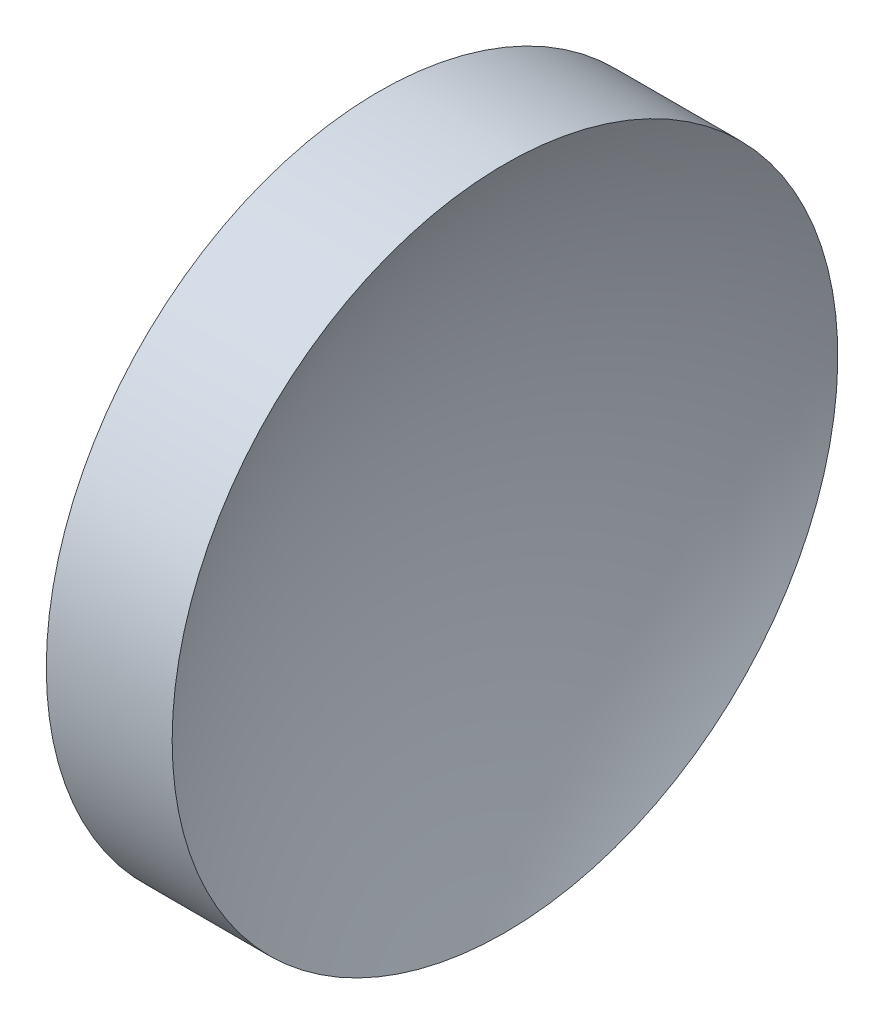
SolidWorks part; units mm, degrees
ref_plane "前视基准面" through (0, 0, 0) normal (0, 0, 1) x (1, 0, 0)
ref_plane "上视基准面" through (0, 0, 0) normal (0, 1, 0) x (1, 0, 0)
ref_plane "右视基准面" through (0, 0, 0) normal (1, 0, 0) x (0, 0, -1)
sketch "草图1" plane through (0, 0, 0) normal (0, 0, 1) x (1, 0, 0)
  line L0 (105.6218, 65.1556) -> (137.1869, 65.1556) construction
  line L1 (113.7394, 65.1556) -> (113.7394, 90.1556)
  line L2 (113.7394, 90.1556) -> (123.1944, 90.1556)
  line L3 (116.7394, 65.1556) -> (113.7394, 65.1556)
  arc A0 (123.1944, 90.1556) -> (116.7394, 65.1556) centre (168.3794, 65.1556) ccw
revolve "旋转1" add sketch "草图1" angle 360 about L0
